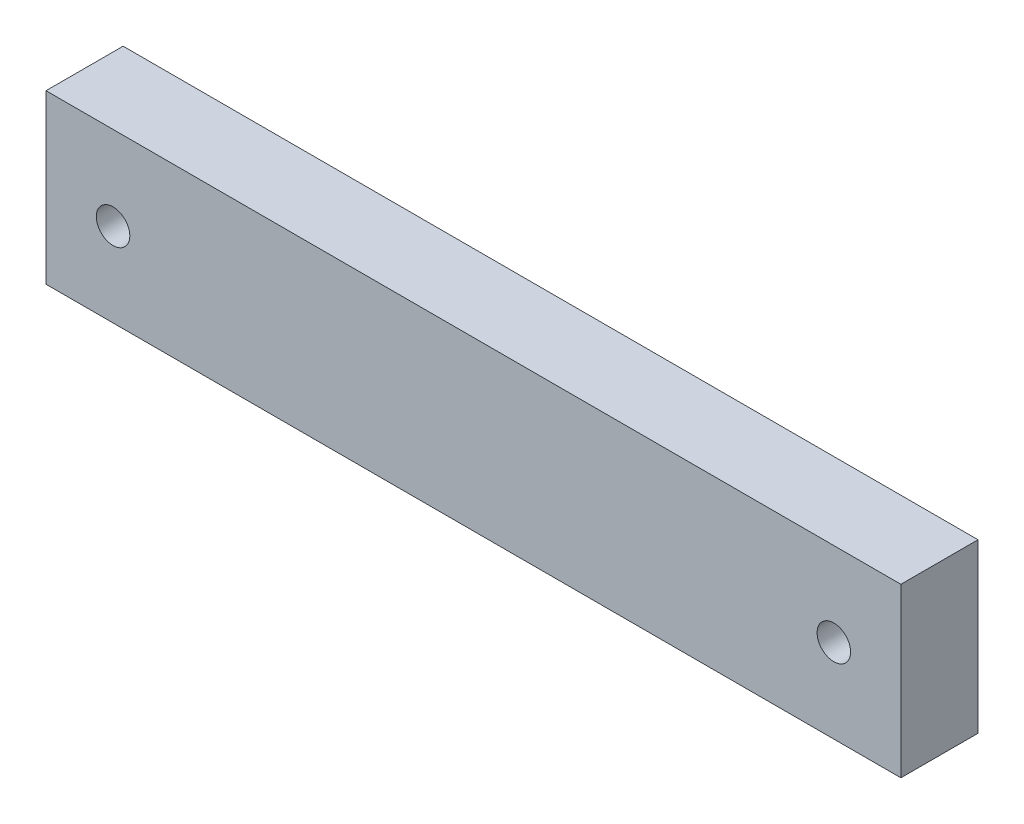
SolidWorks part; units mm, degrees
ref_plane "Front Plane" through (0, 0, 0) normal (0, 0, 1) x (1, 0, 0)
ref_plane "Top Plane" through (0, 0, 0) normal (0, 1, 0) x (1, 0, 0)
ref_plane "Right Plane" through (0, 0, 0) normal (1, 0, 0) x (0, 0, -1)
sketch "Sketch1" plane through (0, 0, 0) normal (0, 0, 1) x (1, 0, 0)
  line L0 (-104.3579, 0) -> (137.9863, 0) construction
  line L1 (-127.5, 25) -> (127.5, 25)
  line L2 (-127.5, 25) -> (-127.5, -25)
  line L3 (-127.5, -25) -> (127.5, -25)
  line L4 (127.5, 25) -> (127.5, -25)
  line L5 (-127.5, 25) -> (127.5, -25) construction
  line L6 (-127.5, -25) -> (127.5, 25) construction
  circle A0 centre (-107.5, 0) radius 5
  circle A1 centre (107.5, 0) radius 5
  point P0 (0, 0)
  dimension "D3" = 10
  dimension "D5" = 20
  dimension "D1" = 255
  dimension "D2" = 50
  dimension "D4" = 20
extrude "Boss-Extrude2" add sketch "Sketch1" along normal blind 23
